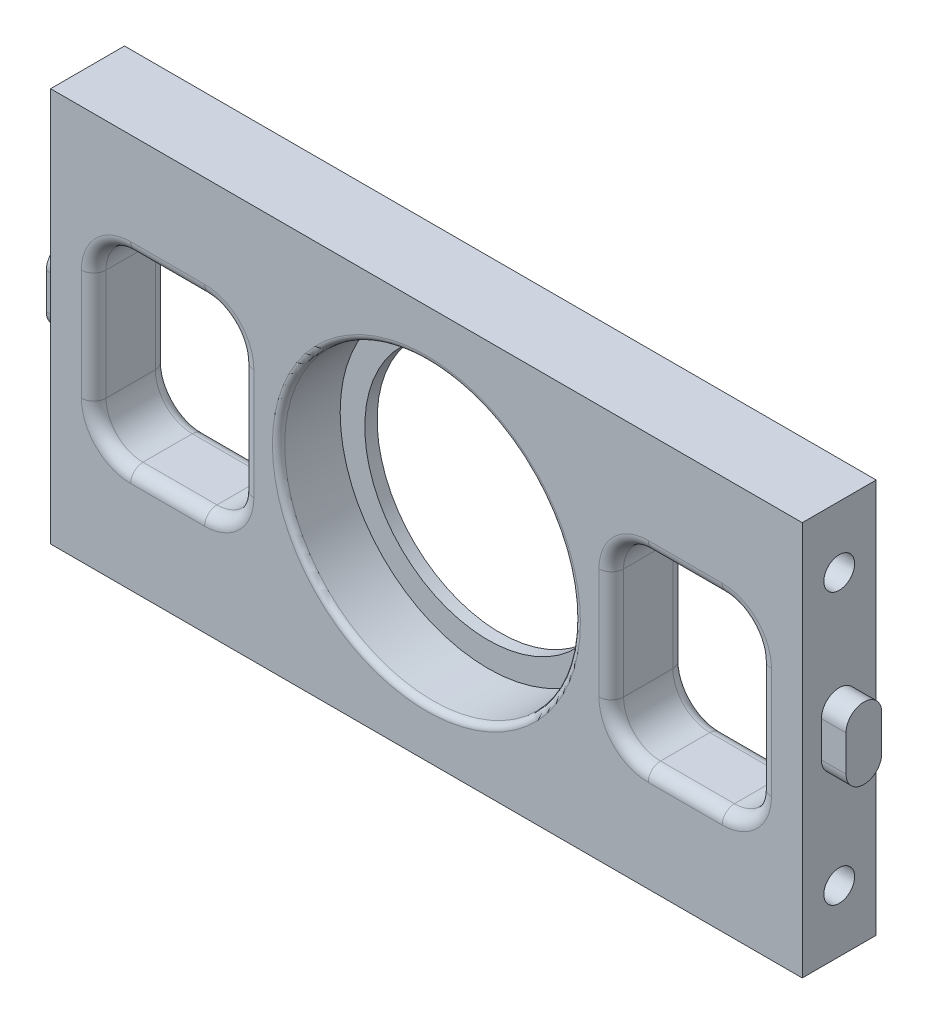
SolidWorks part; units mm, degrees
ref_plane "Спереди" through (0, 0, 0) normal (0, 0, 1) x (1, 0, 0)
ref_plane "Сверху" through (0, 0, 0) normal (0, 1, 0) x (1, 0, 0)
ref_plane "Справа" through (0, 0, 0) normal (1, 0, 0) x (0, 0, -1)
sketch "Эскиз1" plane through (0, 0, 0) normal (0, 0, 1) x (1, 0, 0)
  line L1 (-30.5, 16) -> (30.5, 16)
  line L2 (-30.5, 16) -> (-30.5, -16)
  line L3 (-30.5, -16) -> (30.5, -16)
  line L4 (30.5, 16) -> (30.5, -16)
  line L5 (-30.5, 16) -> (30.5, -16) construction
  line L6 (-30.5, -16) -> (30.5, 16) construction
  circle A0 centre (0, 0) radius 10
  circle A1 centre (0, 0) radius 12
  point P0 (0, 0)
  dimension "D3" = 20
  dimension "D4" = 24
  dimension "D1" = 32
  dimension "D2" = 61
extrude "Бобышка-Вытянуть1" add sketch "Эскиз1" along normal blind 6 contours L1 L4 L3 L2
sketch "Эскиз2" plane through (0, 0, 6) normal (0, 0, 1) x (1, 0, 0)
  circle A0 centre (0, 0) radius 10
  dimension "D1" = 20
extrude "Вырез-Вытянуть13" cut sketch "Эскиз2" against normal blind 6
sketch "Эскиз4" plane through (0, 0, 6) normal (0, 0, 1) x (1, 0, 0)
  circle A0 centre (0, 0) radius 12
extrude "Вырез-Вытянуть14" cut sketch "Эскиз4" against normal blind 5
sketch "Эскиз5" plane through (0, 0, 6) normal (0, 0, 1) x (1, 0, 0)
  line L0 (7.1913, 1.253) -> (19.1913, -13.747)
  line L1 (-18, -7.5) -> (-24, -7.5)
  line L2 (-15, -4.5) -> (-15, 4.5)
  line L3 (-18, 7.5) -> (-24, 7.5)
  line L4 (-27, -4.5) -> (-27, 4.5)
  line L5 (-15, -7.5) -> (-27, 7.5) construction
  line L6 (-15, 7.5) -> (-27, -7.5) construction
  line L7 (18, 7.5) -> (24, 7.5)
  line L8 (15, 4.5) -> (15, -4.5)
  line L9 (18, -7.5) -> (24, -7.5)
  line L10 (27, 4.5) -> (27, -4.5)
  line L11 (15, 7.5) -> (27, -7.5) construction
  line L12 (15, -7.5) -> (27, 7.5) construction
  line L13 (22.8087, 13.747) -> (34.8087, -1.253)
  line L14 (-7.1913, -1.253) -> (-19.1913, 13.747)
  line L15 (-22.8087, -13.747) -> (-34.8087, 1.253)
  arc A0 (27, 4.5) -> (24, 7.5) centre (24, 4.5) ccw
  arc A1 (27, -4.5) -> (24, -7.5) centre (24, -4.5) cw
  arc A2 (18, -7.5) -> (15, -4.5) centre (18, -4.5) cw
  arc A3 (18, 7.5) -> (15, 4.5) centre (18, 4.5) ccw
  arc A4 (-27, -4.5) -> (-24, -7.5) centre (-24, -4.5) ccw
  arc A5 (-15, -4.5) -> (-18, -7.5) centre (-18, -4.5) cw
  arc A6 (-15, 4.5) -> (-18, 7.5) centre (-18, 4.5) ccw
  arc A7 (-24, 7.5) -> (-27, 4.5) centre (-24, 4.5) ccw
  point P0 (-21, 0)
  point P5 (21, 0)
  dimension "D9" = 3
  dimension "D1" = 12
  dimension "D2" = 15
  dimension "D3" = 12
  dimension "D4" = 15
  dimension "D5" = 10
  dimension "D6" = 10
  dimension "D7" = 10
  dimension "D8" = 10
extrude "Вырез-Вытянуть16" cut sketch "Эскиз5" against normal blind 6 contours L10 L7 L8 L9 | L4 L1 L2 L3
sketch "Эскиз8" plane through (-30.5, 0, 0) normal (-1, 0, 0) x (0, 0, 1)
  line L0 (2.9, -1.5) -> (2.9, 1.4) construction
  line L1 (1.45, -1.5) -> (1.45, 1.4)
  line L2 (4.35, -1.5) -> (4.35, 1.4)
  arc A0 (1.45, -1.5) -> (4.35, -1.5) centre (2.9, -1.5) ccw
  arc A1 (4.35, 1.4) -> (1.45, 1.4) centre (2.9, 1.4) ccw
  point P2 (2.9, -0.05)
extrude "Бобышка-Вытянуть12" add sketch "Эскиз8" along normal blind 2
sketch "Эскиз9" plane through (30.5, 0, 0) normal (1, 0, 0) x (0, 0, -1)
  line L0 (-3, 1.45) -> (-3, -1.45) construction
  line L1 (-1.55, 1.45) -> (-1.55, -1.45)
  line L2 (-4.45, 1.45) -> (-4.45, -1.45)
  arc A0 (-1.55, 1.45) -> (-4.45, 1.45) centre (-3, 1.45) ccw
  arc A1 (-4.45, -1.45) -> (-1.55, -1.45) centre (-3, -1.45) ccw
  point P2 (-3, 0)
extrude "Бобышка-Вытянуть13" add sketch "Эскиз9" along normal blind 2
sketch "Эскиз10" plane through (-30.5, 0, 0) normal (-1, 0, 0) x (0, 0, 1)
  line L0 (-20.0331, 0) -> (25.7005, 0) construction
  circle A0 centre (3, 11) radius 1.25
  circle A1 centre (3, -11) radius 1.25
  dimension "D1" = 11
  dimension "D2" = 2.5
  dimension "D3" = 3
extrude "Вырез-Вытянуть18" cut sketch "Эскиз10" against normal blind 15
sketch "Эскиз11" plane through (30.5, 0, 0) normal (1, 0, 0) x (0, 0, -1)
  line L1 (-28.5289, 0) -> (21.2588, 0) construction
  circle A0 centre (-3, 11) radius 1.25
  circle A1 centre (-3, -11) radius 1.25
  dimension "D2" = 11
  dimension "D4" = 2.5
  dimension "D3" = 3
extrude "Вырез-Вытянуть19" cut sketch "Эскиз11" against normal blind 15
fillet "Скругление1" radius 1 32 edges at (-15.8787, -6.6213, 0) (-21, -7.5, 0) (-26.1213, -6.6213, 0) (-27, 0, 0) (-26.1213, 6.6213, 0) (-21, 7.5, 0) (-15.8787, 6.6213, 0) (-15, 0, 0) (-15, 0, 6) (-15.8787, -6.6213, 6) (-26.1213, -6.6213, 6) (-26.1213, 6.6213, 6) (-27, 0, 6) (-21, -7.5, 6) (-15.8787, 6.6213, 6) (-21, 7.5, 6) (21, -7.5, 0) (26.1213, 6.6213, 0) (27, 0, 0) (26.1213, -6.6213, 0) (15.8787, -6.6213, 0) (15, 0, 0) (15.8787, 6.6213, 0) (21, 7.5, 0) (15.8787, 6.6213, 6) (15, 0, 6) (15.8787, -6.6213, 6) (21, -7.5, 6) (26.1213, -6.6213, 6) (27, 0, 6) (26.1213, 6.6213, 6) (21, 7.5, 6)
fillet "Скругление2" radius 0.5 1 edges at (12, 0, 6)
